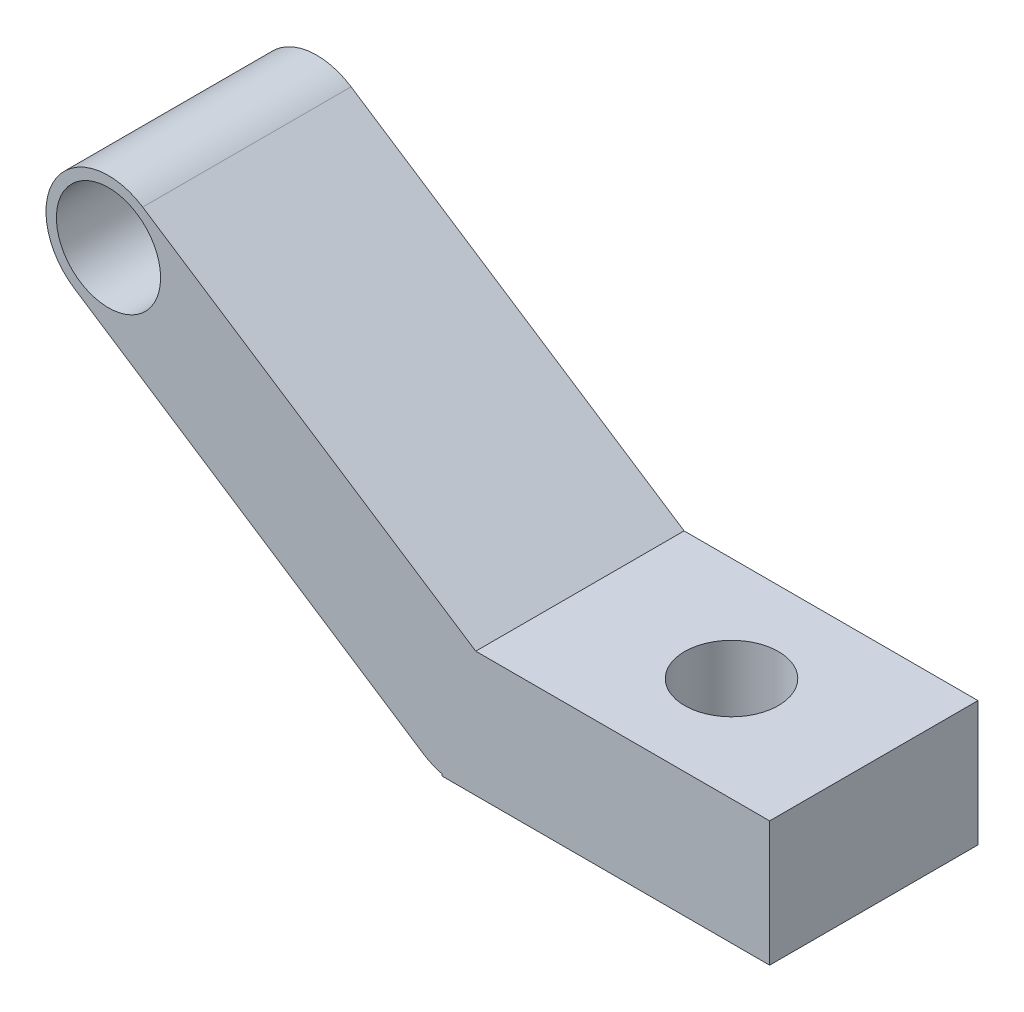
SolidWorks part; units mm, degrees
ref_plane "Front Plane" through (0, 0, 0) normal (0, 0, 1) x (1, 0, 0)
ref_plane "Top Plane" through (0, 0, 0) normal (0, 1, 0) x (1, 0, 0)
ref_plane "Right Plane" through (0, 0, 0) normal (1, 0, 0) x (0, 0, -1)
sketch "Sketch2" plane through (0, 0, 0) normal (0, 0, 1) x (1, 0, 0)
  line L0 (0, 0) -> (-334.6244, 219.1495) construction
  line L1 (-32.8724, -50.1937) -> (-367.4968, 168.9559)
  line L2 (32.8724, 50.1937) -> (-301.752, 269.3432)
  arc A0 (-32.8724, -50.1937) -> (32.8724, 50.1937) centre (0, 0) ccw
  arc A1 (-301.752, 269.3432) -> (-367.4968, 168.9559) centre (-334.6244, 219.1495) ccw
  circle A2 centre (-334.6244, 219.1495) radius 50
  point P3 (-167.3122, 109.5748)
  dimension "D1" = 100
  dimension "D3" = 60
  dimension "D2" = 400
extrude "Boss-Extrude1" add sketch "Sketch2" along normal blind 200
sketch "Sketch4" plane through (0, 0, 200) normal (0, 0, 1) x (1, 0, 0)
  line L1 (-14.3009, -60) -> (300, -60)
  line L3 (-14.3009, 60) -> (300, 60)
  line L4 (300, -60) -> (300, 60)
  line L5 (-14.3009, -2.8602) -> (300, 60) construction
  line L6 (-14.3009, 2.8602) -> (300, -60) construction
  line L7 (-14.3009, 60) -> (-14.3009, -60)
  point P0 (0, 0)
  dimension "D1" = 314.3009
  dimension "D2" = 120
extrude "Boss-Extrude2" add sketch "Sketch4" against normal blind 200
sketch "Sketch7" plane through (0, 60, 0) normal (0, 1, 0) x (1, 0, 0)
  circle A0 centre (163.3993, -100) radius 45
  dimension "D1" = 90
extrude "Cut-Extrude1" cut sketch "Sketch7" against normal through all contours A0
